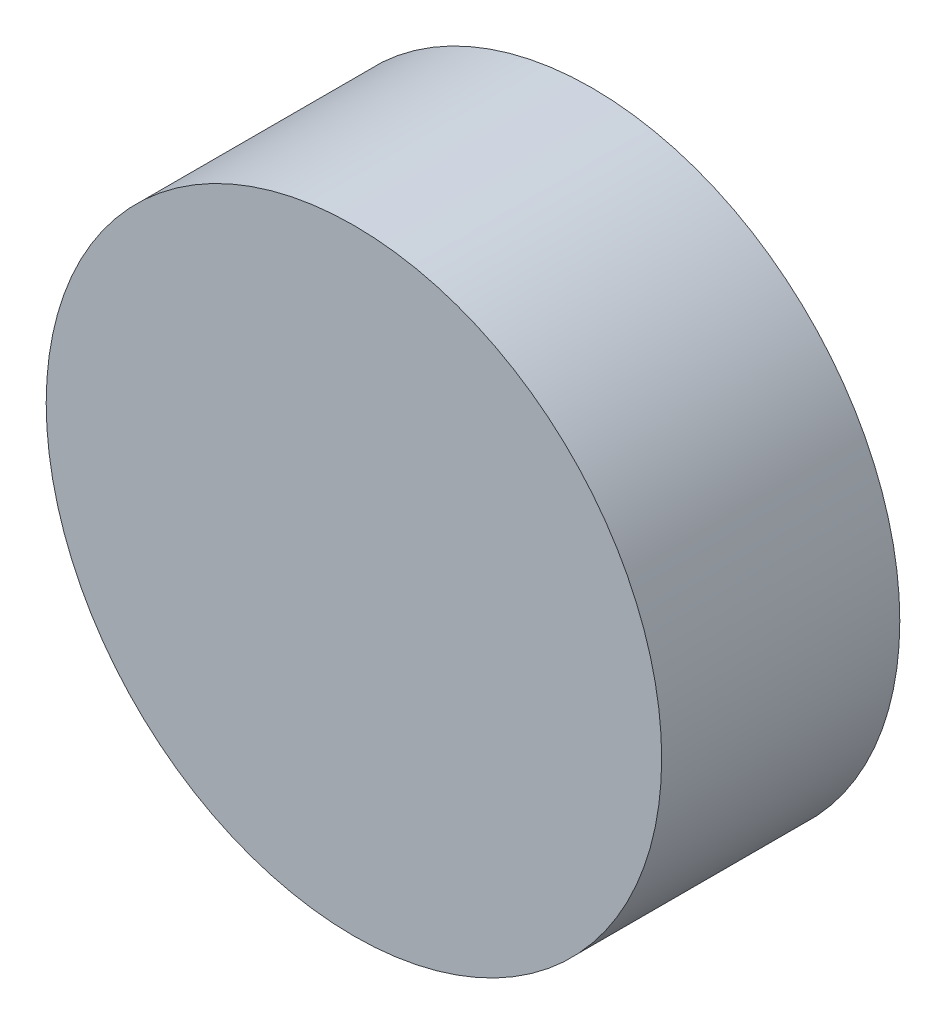
SolidWorks part; units mm, degrees
ref_plane "Front Plane" through (0, 0, 0) normal (0, 0, 1) x (1, 0, 0)
ref_plane "Top Plane" through (0, 0, 0) normal (0, 1, 0) x (1, 0, 0)
ref_plane "Right Plane" through (0, 0, 0) normal (1, 0, 0) x (0, 0, -1)
sketch "Sketch1" plane through (0, 0, 0) normal (0, 0, 1) x (1, 0, 0)
  circle A0 centre (0, 0) radius 33.6
  dimension "D1" = 67.2
extrude "Boss-Extrude1" add sketch "Sketch1" along normal blind 26
sketch "Sketch2" plane through (0, 0, 0) normal (0, 0, -1) x (-1, 0, 0)
  circle A0 centre (0, 0) radius 6.35
  dimension "D1" = 12.7
extrude "Boss-Extrude2" add sketch "Sketch2" along normal blind 4.572
